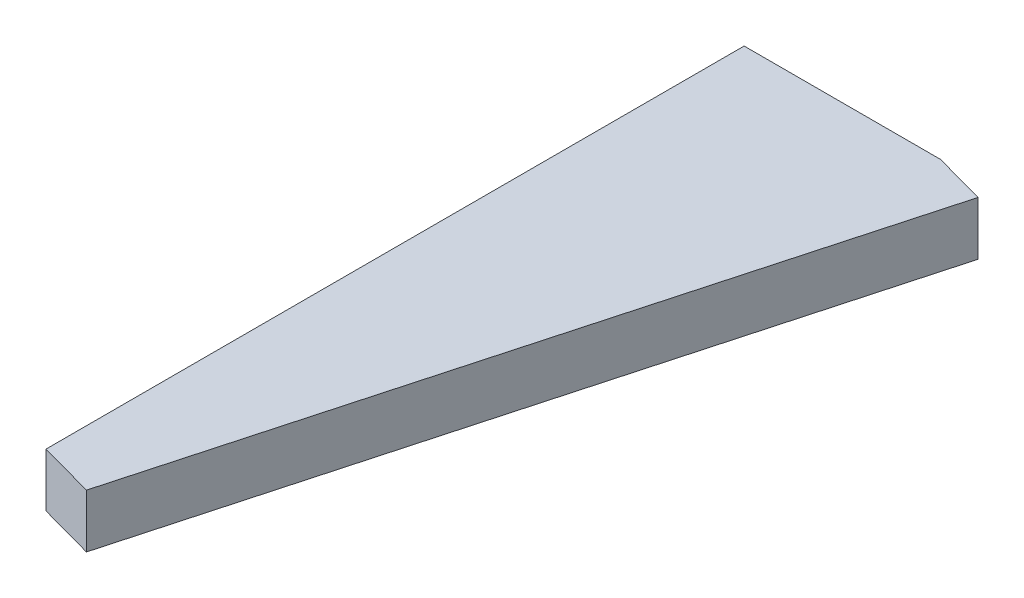
SolidWorks part; units mm, degrees
ref_plane "Front Plane" through (0, 0, 0) normal (0, 0, 1) x (1, 0, 0)
ref_plane "Top Plane" through (0, 0, 0) normal (0, 1, 0) x (1, 0, 0)
ref_plane "Right Plane" through (0, 0, 0) normal (1, 0, 0) x (0, 0, -1)
sketch "Sketch1" plane through (0, 0, 0) normal (0, 1, 0) x (1, 0, 0)
  line L0 (11, 40) -> (40.0966, 31.9984) construction
  line L1 (13.8926, 39.2045) -> (11, 40)
  line L2 (0, 0.9023) -> (0, 40)
  line L3 (0, 40) -> (11, 40)
  line L4 (3.1233, 0.0434) -> (0, 0.9023)
  line L5 (11, 40) -> (0, 0) construction
  line L6 (13.8926, 39.2045) -> (3.1233, 0.0434)
  line L7 (2.8926, -0.7955) -> (0, 0) construction
  line L9 (13.8926, 39.2045) -> (2.8926, -0.7955) construction
  dimension "D1" = 11
  dimension "D2" = 40
  dimension "D3" = 90
  dimension "D5" = 3.2393
  dimension "D6" = 90
  dimension "D4" = 3
extrude "Boss-Extrude2" add sketch "Sketch1" along normal blind 3 contours L4 L2 L3 L1 L6
